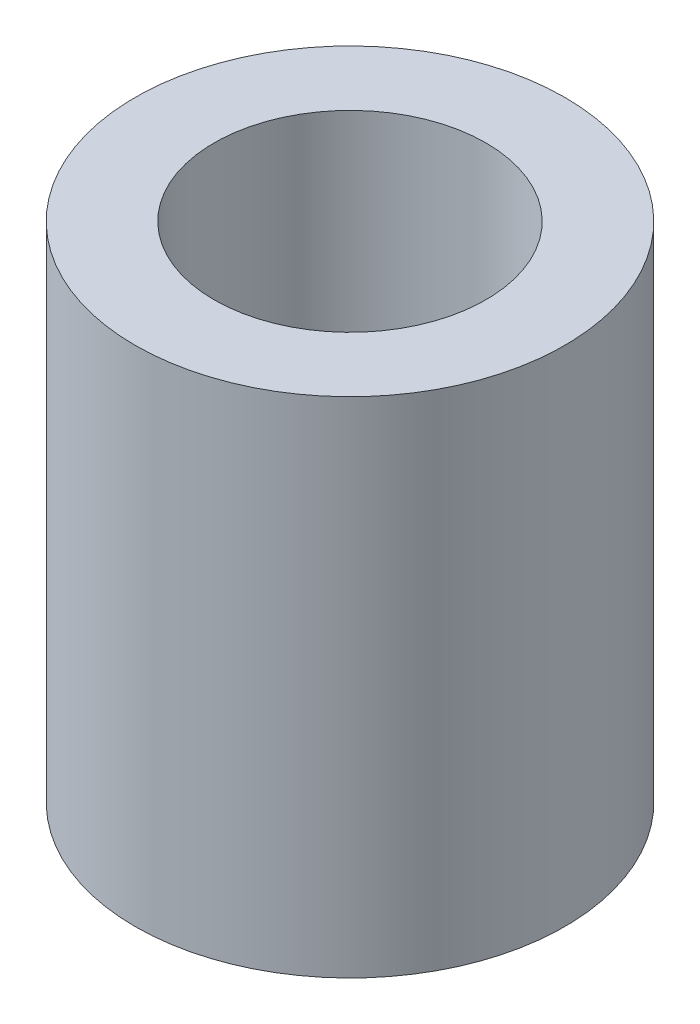
SolidWorks part; units mm, degrees
ref_plane "Front Plane" through (0, 0, 0) normal (0, 0, 1) x (1, 0, 0)
ref_plane "Top Plane" through (0, 0, 0) normal (0, 1, 0) x (1, 0, 0)
ref_plane "Right Plane" through (0, 0, 0) normal (1, 0, 0) x (0, 0, -1)
sketch "Sketch2" plane through (0, 0, 0) normal (0, 1, 0) x (1, 0, 0)
  circle A0 centre (0, 0) radius 2.025
  circle A1 centre (0, 0) radius 3.2
  dimension "D1" = 4.05
  dimension "D2" = 6.4
extrude "Boss-Extrude1" add sketch "Sketch2" along normal blind 7.5
